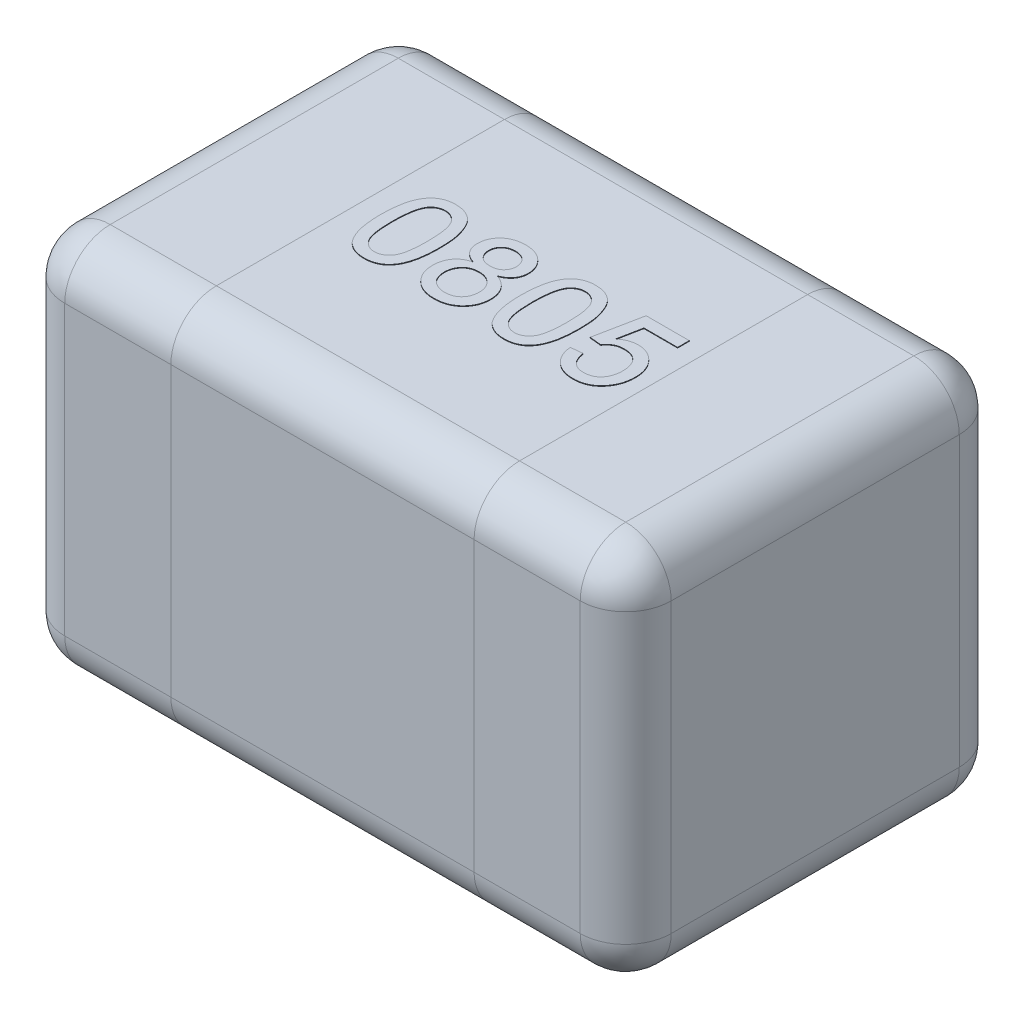
SolidWorks part; units mm, degrees
ref_plane "Front" through (0, 0, 0) normal (0, 0, 1) x (1, 0, 0)
ref_plane "Top" through (0, 0, 0) normal (0, 1, 0) x (1, 0, 0)
ref_plane "Right" through (0, 0, 0) normal (1, 0, 0) x (0, 0, -1)
sketch "Sketch1" plane through (0, 0, 0) normal (0, 1, 0) x (1, 0, 0)
  line L0 (0, -5.3126) -> (0, 5.729) construction
  line L1 (-6.1479, 0) -> (7.7291, 0) construction
  line L3 (-1, 0.625) -> (1, 0.625)
  line L4 (-1, 0.625) -> (-1, -0.625)
  line L5 (-1, -0.625) -> (1, -0.625)
  line L6 (1, 0.625) -> (1, -0.625)
  dimension "D1" = 2
  dimension "D2" = 1.25
extrude "Extrude1" add sketch "Sketch1" along normal blind 1.25
fillet "Fillet1" radius 0.15 12 edges at (0, 1.25, 0.625) (-1, 0.625, -0.625) (0, 0, -0.625) (-1, 0, 0) (-1, 0.625, 0.625) (0, 0, 0.625) (1, 0.625, 0.625) (1, 0.625, -0.625) (1, 0, 0) (0, 1.25, -0.625) (1, 1.25, 0) (-1, 1.25, 0)
sketch "Sketch2" plane through (0, 0, 0.625) normal (0, 0, 1) x (1, 0, 0)
  line L0 (-0.85, 1.25) -> (0.85, 1.25) construction
  line L1 (-0.5, 1.25) -> (0.5, 1.25)
  line L2 (-0.5, 1.25) -> (-0.5, 0)
  line L3 (-0.5, 0) -> (0.5, 0)
  line L4 (0.5, 1.25) -> (0.5, 0)
  line L5 (0.85, 0) -> (-0.85, 0) construction
  line L6 (-1, 0.15) -> (-1, 1.1) construction
  line L7 (0, -0.2963) -> (0, 3.0124) construction
  dimension "D1" = 0.5
split line "Split Line1"
sketch "Sketch3" plane through (0, 1.25, 0) normal (0, 1, 0) x (1, 0, 0)
  text T0 "0805" font "Arial" height 0.3
  dimension "D1" = 0.45
  dimension "D2" = 0.15
extrude "Extrude2" add sketch "Sketch3" along normal blind 0.002
